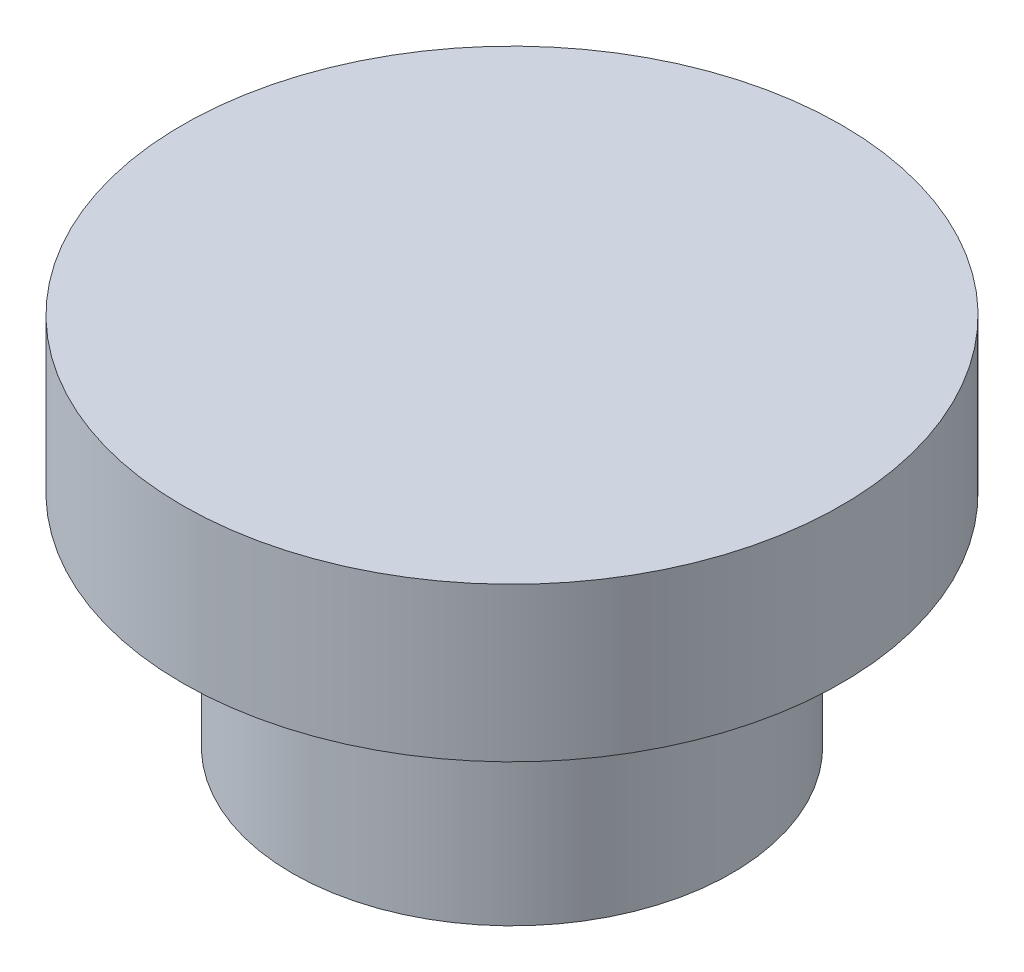
SolidWorks part; units mm, degrees
ref_plane "前视基准面" through (0, 0, 0) normal (0, 0, 1) x (1, 0, 0)
ref_plane "上视基准面" through (0, 0, 0) normal (0, 1, 0) x (1, 0, 0)
ref_plane "右视基准面" through (0, 0, 0) normal (1, 0, 0) x (0, 0, -1)
sketch "草图1" plane through (0, 0, 0) normal (0, 1, 0) x (1, 0, 0)
  circle A0 centre (0, 0) radius 15
  dimension "D1" = 30
extrude "凸台-拉伸1" add sketch "草图1" along normal blind 7
sketch "草图2" plane through (0, 0, 0) normal (0, -1, 0) x (-1, 0, 0)
  circle A0 centre (0, 0) radius 10
  dimension "D1" = 20
extrude "凸台-拉伸2" add sketch "草图2" along normal blind 10
